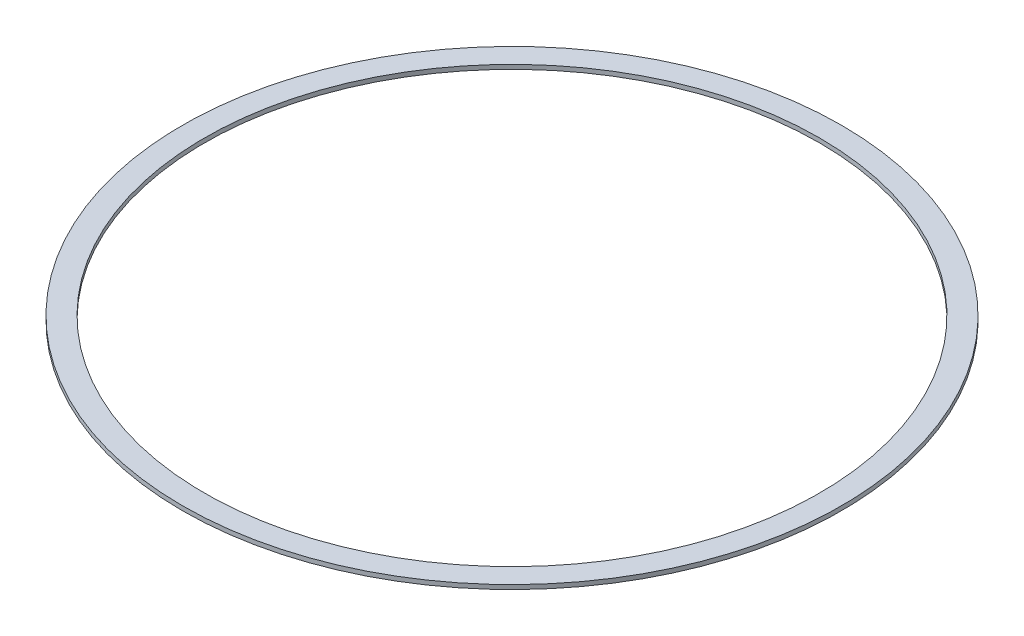
SolidWorks part; units mm, degrees
ref_plane "Front Plane" through (0, 0, 0) normal (0, 0, 1) x (1, 0, 0)
ref_plane "Top Plane" through (0, 0, 0) normal (0, 1, 0) x (1, 0, 0)
ref_plane "Right Plane" through (0, 0, 0) normal (1, 0, 0) x (0, 0, -1)
sketch "Sketch1" plane through (0, 0, 0) normal (0, 0, 1) x (1, 0, 0)
  line L0 (0, 0) -> (0, 46.8686) construction
  line L1 (71.12, 23.4343) -> (71.12, 22.4343)
  line L2 (71.12, 22.4343) -> (76.2, 22.4343)
  line L3 (76.2, 22.4343) -> (76.2, 23.4343)
  line L4 (76.2, 23.4343) -> (71.12, 23.4343)
  line L5 (71.12, 22.9343) -> (0, 22.9343) construction
  dimension "D1" = 5.08
  dimension "D2" = 1
  dimension "D3" = 71.12
revolve "Revolve1" add sketch "Sketch1" angle 360 about L0
